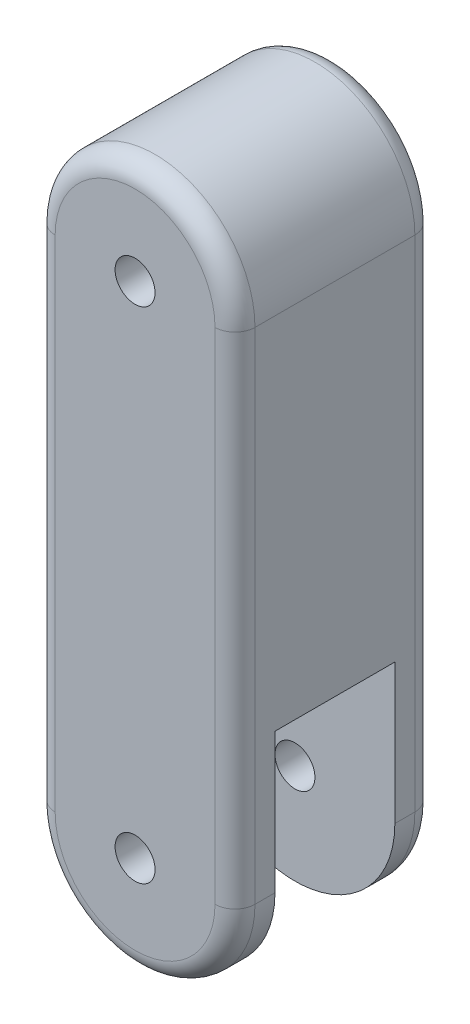
SolidWorks part; units mm, degrees
ref_plane "Alzado" through (0, 0, 0) normal (0, 0, 1) x (1, 0, 0)
ref_plane "Planta" through (0, 0, 0) normal (0, 1, 0) x (1, 0, 0)
ref_plane "Vista lateral" through (0, 0, 0) normal (1, 0, 0) x (0, 0, -1)
sketch "Croquis1" plane through (0, 0, 0) normal (0, 0, 1) x (1, 0, 0)
  line L0 (-2.5, 0) -> (-2.5, -12.5)
  line L3 (2.5, 0) -> (2.5, -12.5)
  line L7 (-2.5, -12.5) -> (-2.5, -10)
  line L8 (-2.5, -10) -> (2.5, -15) construction
  circle A0 centre (0, 0) radius 0.5
  arc A1 (2.5, 0) -> (-2.5, 0) centre (0, 0) ccw
  circle A2 centre (0, -12.5) radius 0.5
  arc A3 (-2.5, -12.5) -> (2.5, -12.5) centre (0, -12.5) ccw
  dimension "D1" = 1
  dimension "D2" = 5
  dimension "D8" = 1
  dimension "D6" = 15
extrude "Saliente-Extruir2" add sketch "Croquis1" along normal blind 5 contours L0 L8 A2 A3 L3 A1 A0 | L8 L0 A3 A2
sketch "Croquis3" plane through (2.5, 0, 0) normal (1, 0, 0) x (0, 0, -1)
  line L0 (-5, -12.5) -> (-5, -9)
  line L1 (-5, 0) -> (-5, -12.5) construction
  line L2 (-5, -9) -> (0, -9)
  line L3 (0, 0) -> (0, -12.5) construction
  line L4 (0, -9) -> (0, -15.6212)
  line L5 (0, -15.6212) -> (-1, -15.6212)
  line L6 (-1, -15.6212) -> (-1, -9)
  line L7 (-4, -9) -> (-4, -15.6212)
  line L8 (-4, -15.6212) -> (-5, -15.6212)
  line L9 (-5, -15.6212) -> (-5, -9)
  line L10 (-4, -15.6212) -> (-1, -15.6212)
  line M8 (-5, -12.5) -> (0, -12.5)
  dimension "D1" = 1
  dimension "D2" = 1
  dimension "D3" = 3.5
extrude "Cortar-Extruir2" cut sketch "Croquis3" against normal blind 5 contours L2 L7 L6 M8 | L7 L10 L6 M8
fillet "Redondeo1" radius 0.5 4 edges at (-2.5, -6.25, 5) (0, -15, 5) (2.5, -6.25, 5) (0, 2.5, 5)
fillet "Redondeo2" radius 0.5 4 edges at (-2.5, -6.25, 0) (0, 2.5, 0) (2.5, -6.25, 0) (0, -15, 0)
